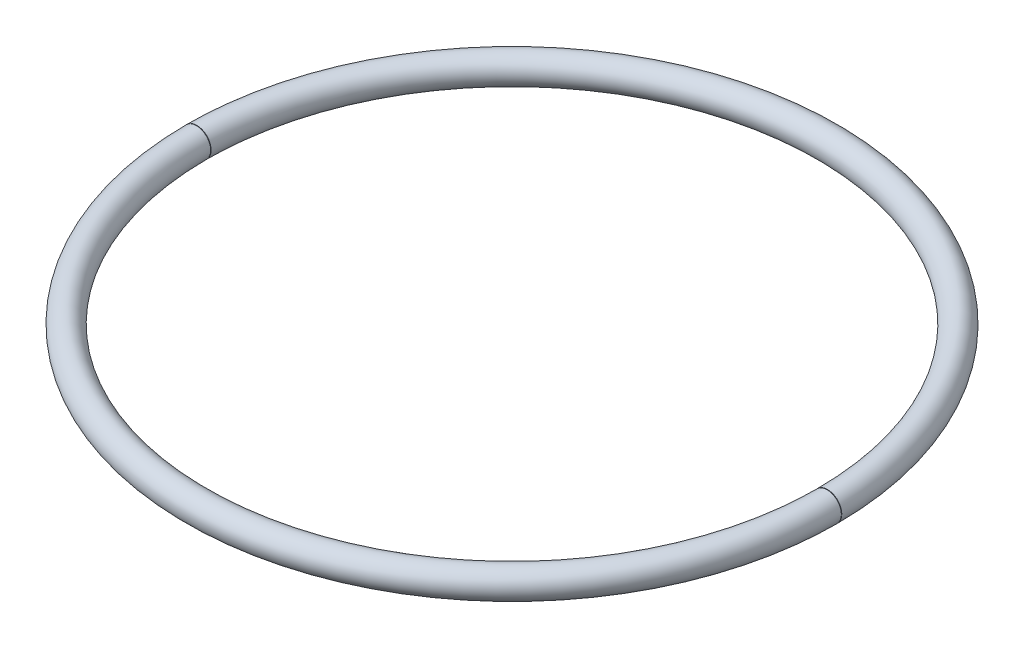
SolidWorks part; units mm, degrees
material "6061 Alloy"
ref_plane "Front Plane" through (0, 0, 0) normal (0, 0, 1) x (1, 0, 0)
ref_plane "Top Plane" through (0, 0, 0) normal (0, 1, 0) x (1, 0, 0)
ref_plane "Right Plane" through (0, 0, 0) normal (1, 0, 0) x (0, 0, -1)
sketch "Sketch1" plane through (0, 0, 0) normal (0, 1, 0) x (1, 0, 0)
  line L1 (758.825, -0.3969) -> (809.625, -0.3969)
  line L2 (758.825, -0.3969) -> (758.825, 0.3969)
  line L3 (758.825, 0.3969) -> (809.625, 0.3969)
  line L4 (809.625, -0.3969) -> (809.625, 0.3969)
  line L5 (758.825, -0.3969) -> (809.625, 0.3969) construction
  line L6 (758.825, 0.3969) -> (809.625, -0.3969) construction
  circle A0 centre (0, 0) radius 784.225
  point P3 (784.225, 0)
  dimension "D1" = 1568.45
  dimension "D2" = 50.8
  dimension "D3" = 0.7937
sketch "Sketch25" plane through (0, 0, 0) normal (0, 1, 0) x (1, 0, 0)
  line L0 (758.825, 0.3969) -> (809.625, 0.3969) construction
  line L1 (588.9625, 0.3969) -> (538.1625, 0.3969)
  line L2 (588.9625, 0.3969) -> (588.9625, -0.3969)
  line L3 (588.9625, -0.3969) -> (538.1625, -0.3969)
  line L4 (538.1625, 0.3969) -> (538.1625, -0.3969)
  line L5 (588.9625, 0.3969) -> (538.1625, -0.3969) construction
  line L6 (588.9625, -0.3969) -> (538.1625, 0.3969) construction
  circle A0 centre (0, 0) radius 563.5625
  point P3 (563.5625, 0)
  point P10 (538.1625, 0)
  point P11 (588.9625, 0)
  dimension "D1" = 1127.125
  dimension "D2" = 50.8
  dimension "D3" = 50.8
  dimension "D4" = 588.9625
sketch "Sketch26" plane through (0, 0, 0) normal (0, 1, 0) x (1, 0, 0)
  line L2 (588.9625, -0.3969) -> (538.1625, -0.3969) construction
  line L4 (588.9625, 0.3969) -> (538.1625, 0.3969) construction
  circle A0 centre (0, 0) radius 563.5625 construction
  arc A1 (563.5624, 0.3969) -> (563.5624, -0.3969) centre (0, 0) ccw
sweep "Sweep4" add path "Sketch26" circular profile diameter 50.8 parameters "D3"=50.8
shell "Shell2" thickness 3.175
sketch "Sketch27" plane through (0, 0, 0) normal (0, 1, 0) x (1, 0, 0)
  line L6 (-609.6, -0.379) -> (-508, -0.379)
  line L7 (-609.6, -0.379) -> (-609.6, 0.379)
  line L9 (-609.6, 0.379) -> (-508, 0.379)
  line L10 (-508, -0.379) -> (-508, 0.379)
  line L11 (-558.8, 0.379) -> (-558.8, -0.379) construction
  line L12 (-609.6, 0) -> (-508, 0) construction
  point P0 (-558.8, 0)
  dimension "D1" = 101.6
  dimension "D2" = 508
extrude "Cut-Extrude1" cut sketch "Sketch27" against normal through all both and the other way through all
